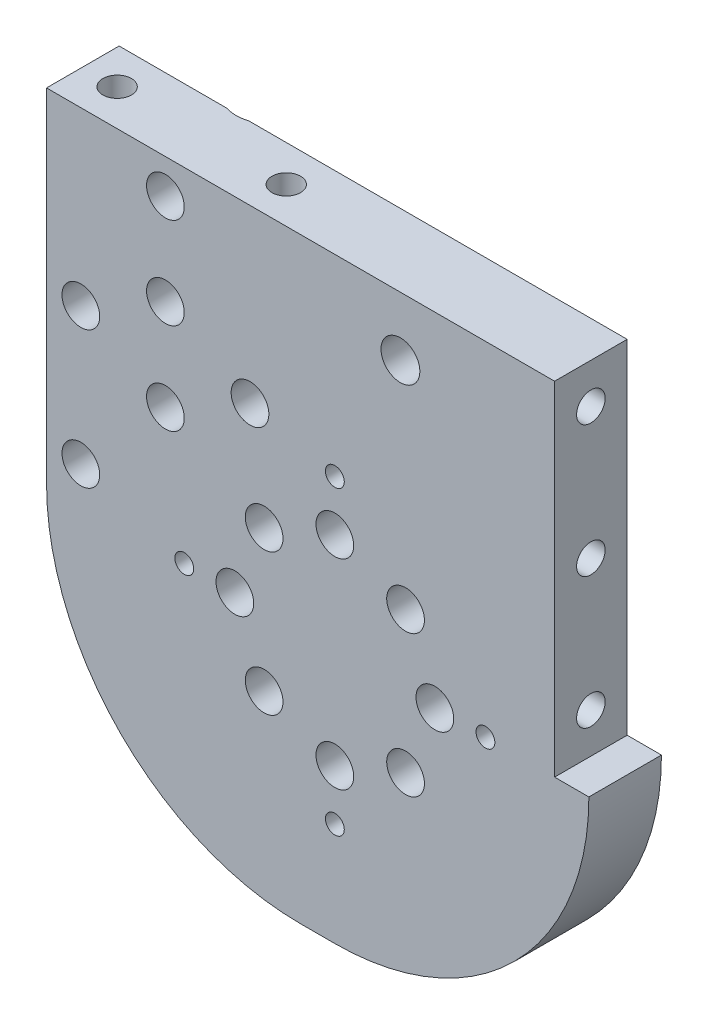
SolidWorks part; units mm, degrees
ref_plane "Front Plane" through (0, 0, 0) normal (0, 0, 1) x (1, 0, 0)
ref_plane "Top Plane" through (0, 0, 0) normal (0, 1, 0) x (1, 0, 0)
ref_plane "Right Plane" through (0, 0, 0) normal (1, 0, 0) x (0, 0, -1)
ref_plane "Plane1" through (0, 0, 0) normal (0, 0, -1) x (-1, 0, 0)
sketch "Sketch1" plane through (0, 0, 0) normal (0, 0, -1) x (-1, 0, 0)
  line L0 (44.45, 0) -> (44.45, 60)
  line L1 (44.45, 60) -> (-44.45, 60)
  line L2 (-44.45, 60) -> (-44.45, 0)
  arc A0 (-44.45, 0) -> (44.45, 0) centre (0, 0) ccw
extrude "Boss-Extrude1" add sketch "Sketch1" against normal blind 12.7
hole_wizard "#4 Clearance Hole1" positions "Sketch3" profile "Sketch2" hole size "#4" standard "ANSI Inch"
sketch "Sketch3" plane through (0, 0, 12.7) normal (0, 0, 1) x (1, 0, 0)
  line L0 (6, 0) -> (6, 26.35) construction
  line L1 (6, 0) -> (32.35, 0) construction
  line L2 (6, 0) -> (6, -26.35) construction
  line L3 (6, 0) -> (-20.35, 0) construction
  circle A0 centre (6, 0) radius 26.35 construction
  point P0 (32.35, 0.009)
  point P1 (6, -26.35)
  point P2 (-20.35, -0.01)
  point P3 (6, 26.35)
  dimension "D1" = 52.7
  dimension "D2" = 6
sketch "Sketch2" plane through (32.35, 0.009, 12.7) normal (1, 0, 0) x (0, -1, 0)
  line L0 (0, 0) -> (0, 12.7)
  line L1 (0, 12.7) -> (1.65, 12.7)
  line L2 (1.65, 12.7) -> (1.65, 0)
  line L5 (1.65, 0) -> (0, 0)
  line L11 (0, -6.35) -> (0, 107.95) construction
  dimension "Thru Hole Dia." = 3.3
  dimension "Thru Hole Depth" = 12.7
hole_wizard "1/4 Clearance Hole1" positions "Sketch5" profile "Sketch4" hole size "1/4" standard "ANSI Inch"
sketch "Sketch5" plane through (0, 0, 0) normal (0, 0, -1) x (-1, 0, 0)
  point P0 (8.85, 30)
  point P1 (23.65, 38)
  point P2 (23.65, 22)
sketch "Sketch4" plane through (-8.85, 30, 0) normal (1, 0, 0) x (0, 1, 0)
  line L0 (0, 0) -> (0, 12.7)
  line L1 (0, 12.7) -> (3.3, 12.7)
  line L2 (3.3, 12.7) -> (3.3, 0)
  line L5 (3.3, 0) -> (0, 0)
  line L11 (0, -6.35) -> (0, 107.95) construction
  dimension "Thru Hole Dia." = 6.6
  dimension "Thru Hole Depth" = 12.7
hole_wizard "1/4 Clearance Hole2" positions "Sketch7" profile "Sketch6" hole size "1/4" standard "ANSI Inch"
sketch "Sketch7" plane through (0, 0, 12.7) normal (0, 0, 1) x (1, 0, 0)
  line L0 (0, 0) -> (0, 60) construction
  line L1 (-44.45, 60) -> (44.45, 60) construction
  point P0 (17.4725, 49.6929)
  dimension "D1" = 17.4725
sketch "Sketch6" plane through (17.4725, 49.6929, 12.7) normal (1, 0, 0) x (0, -1, 0)
  line L0 (0, 0) -> (0, 12.7)
  line L1 (0, 12.7) -> (3.4, 12.7)
  line L2 (3.4, 12.7) -> (3.4, 0)
  line L5 (3.4, 0) -> (0, 0)
  line L11 (0, -6.35) -> (0, 107.95) construction
  dimension "Thru Hole Dia." = 6.8
  dimension "Thru Hole Depth" = 12.7
hole_wizard "CSK for 1/4 Flat Head Machine Screw (100)1" positions "Sketch9" profile "Sketch8" countersink size "1/4" standard "ANSI Inch"
sketch "Sketch9" plane through (0, 0, 0) normal (0, 0, -1) x (-1, 0, 0)
  point P0 (23.65, 54)
  point P1 (38.45, 6)
  point P2 (38.45, 30)
sketch "Sketch8" plane through (-23.65, 54, 0) normal (1, 0, 0) x (0, 1, 0)
  line L0 (0, 0) -> (0, 12.7)
  line L1 (0, 12.7) -> (3.3, 12.7)
  line L2 (3.3, 12.7) -> (3.3, 3)
  line L3 (3.3, 3) -> (6.3, 0)
  line L5 (6.3, 0) -> (0, 0)
  line L6 (-3.3, 3) -> (-6.3, 0) construction
  line L11 (0, -6.35) -> (0, 107.95) construction
  dimension "Thru Hole Dia." = 6.6
  dimension "Thru Hole Depth" = 12.7
  dimension "Near C'Sink Dia." = 12.6
  dimension "Near C'Sink Angle" = 90
hole_wizard "#10 Clearance Hole1" positions "Sketch11" profile "Sketch10" hole size "#10" standard "ANSI Inch"
sketch "Sketch11" plane through (0, 60, 0) normal (0, 1, 0) x (1, 0, 0)
  point P0 (-38.45, -6.35)
  point P1 (-8.85, -6.35)
sketch "Sketch10" plane through (-38.45, 60, 6.35) normal (1, 0, 0) x (0, 0, 1)
  line L0 (0, 0) -> (0, 15)
  line L1 (0, 15) -> (2.5, 15)
  line L2 (2.5, 15) -> (2.5, 0)
  line L5 (2.5, 0) -> (0, 0)
  line L10 (0, 15) -> (-2.5, 15) construction
  line L11 (0, -6.35) -> (0, 107.95) construction
  dimension "Hole Dia." = 5
  dimension "Hole Depth" = 15
  dimension "Drill Angle" = 180
hole_wizard "#10 Clearance Hole2" positions "Sketch13" profile "Sketch12" hole size "#10" standard "ANSI Inch"
sketch "Sketch13" plane through (44.45, 0, 0) normal (1, 0, 0) x (0, 0, -1)
  point P0 (-6.35, 7)
  point P1 (-6.35, 53)
  point P2 (-6.35, 30)
sketch "Sketch12" plane through (44.45, 7, 6.35) normal (0, 1, 0) x (0, 0, -1)
  line L0 (0, 0) -> (0, 10)
  line L1 (0, 10) -> (2.5, 10)
  line L2 (2.5, 10) -> (2.5, 0)
  line L5 (2.5, 0) -> (0, 0)
  line L10 (0, 10) -> (-2.5, 10) construction
  line L11 (0, -6.35) -> (0, 107.95) construction
  dimension "Hole Dia." = 5
  dimension "Hole Depth" = 10
  dimension "Drill Angle" = 180
hole_wizard "1-3/4 Clearance Hole1" positions "Sketch15" profile "Sketch14" hole size "1-3/4" standard "ANSI Inch"
sketch "Sketch15" plane through (0, 0, 0) normal (0, 0, -1) x (-1, 0, 0)
  point P0 (-6, 0)
  dimension "D1" = 6
sketch "Sketch14" plane through (6, 0, 0) normal (1, 0, 0) x (0, 1, 0)
  line L0 (0, 0) -> (0, 5)
  line L1 (0, 5) -> (22.5, 5)
  line L2 (22.5, 5) -> (22.5, 0)
  line L5 (22.5, 0) -> (0, 0)
  line L10 (0, 5) -> (-22.5, 5) construction
  line L11 (0, -6.35) -> (0, 107.95) construction
  dimension "Hole Dia." = 45
  dimension "Hole Depth" = 5
  dimension "Drill Angle" = 180
hole_wizard "1/4 Clearance Hole3" positions "Sketch17" profile "Sketch16" hole size "1/4" standard "ANSI Inch"
sketch "Sketch17" plane through (0, 0, 12.7) normal (0, 0, 1) x (1, 0, 0)
  line L0 (6, 0) -> (6, 17.5) construction
  line L2 (6, 0) -> (-6.3744, 12.3744) construction
  line L4 (6, 0) -> (-11.5, 0) construction
  line L5 (6, 0) -> (-6.3744, -12.3744) construction
  line L6 (6, 0) -> (6, -17.5) construction
  line L7 (6, 0) -> (18.3744, -12.3744) construction
  line L8 (6, 0) -> (23.5, 0) construction
  line L9 (6, 0) -> (18.3744, 12.3744) construction
  circle A0 centre (6, 0) radius 17.5 construction
  point P0 (18.3744, 12.3744)
  point P1 (23.5, -0.0012)
  point P2 (18.3744, -12.3744)
  point P3 (6, -17.5)
  point P4 (-6.3744, -12.3744)
  point P5 (-11.5, 0)
  point P6 (-6.3744, 12.3744)
  point P7 (6, 17.5)
  dimension "D1" = 35
  dimension "D2" = 45
  dimension "D3" = 45
  dimension "D4" = 45
  dimension "D5" = 45
  dimension "D6" = 6
sketch "Sketch16" plane through (18.3744, 12.3744, 12.7) normal (1, 0, 0) x (0, -1, 0)
  line L0 (0, 0) -> (0, 12.7)
  line L1 (0, 12.7) -> (3.3, 12.7)
  line L2 (3.3, 12.7) -> (3.3, 0)
  line L5 (3.3, 0) -> (0, 0)
  line L11 (0, -6.35) -> (0, 107.95) construction
  dimension "Thru Hole Dia." = 6.6
  dimension "Thru Hole Depth" = 12.7
chamfer "Chamfer1" distance 3 angle 45 3 edges at (-26.95, 38, 0) (-12.15, 30, 0) (-26.95, 22, 0)
sketch "Sketch18" plane through (0, 0, 0) normal (0, 0, -1) x (-1, 0, 0)
  line L0 (44.45, 0) -> (-44.45, 0) construction
  line L1 (-44.45, 0) -> (-50.45, 0)
  line L2 (-6, -44.45) -> (0, -44.45)
  arc A0 (-50.45, 0) -> (-6, -44.45) centre (-6, 0) ccw
  arc A1 (-44.45, 0) -> (44.45, 0) centre (0, 0) ccw construction
  arc A2 (-44.45, 0) -> (0, -44.45) centre (0, 0) ccw
  dimension "D1" = 88.9
extrude "Boss-Extrude2" add sketch "Sketch18" against normal up to surface (12.7 mm away) up to face at (21.6744, 12.3744, 12.7)
